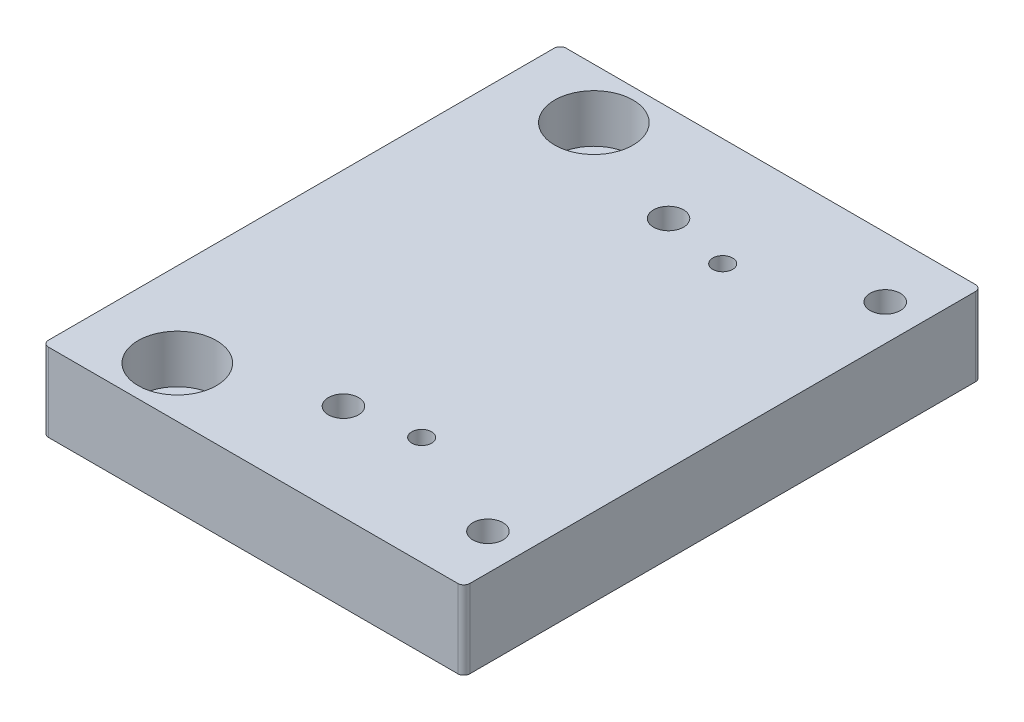
SolidWorks part; units mm, degrees
ref_plane "Front Plane" through (0, 0, 0) normal (0, 0, 1) x (1, 0, 0)
ref_plane "Top Plane" through (0, 0, 0) normal (0, 1, 0) x (1, 0, 0)
ref_plane "Right Plane" through (0, 0, 0) normal (1, 0, 0) x (0, 0, -1)
sketch "Sketch1" plane through (0, 0, 0) normal (0, 1, 0) x (1, 0, 0)
  line L1 (0, 0) -> (70, 0)
  line L2 (0, 0) -> (0, -86)
  line L3 (0, -86) -> (70, -86)
  line L4 (70, 0) -> (70, -86)
  dimension "D1" = 70
  dimension "D2" = 86
extrude "Boss-Extrude1" add sketch "Sketch1" along normal blind 5
sketch "Sketch2" plane through (0, 5, 0) normal (0, 1, 0) x (1, 0, 0)
  line L0 (0, -86) -> (70, -86) construction
  line L1 (70, 0) -> (58, 0)
  line L2 (70, 0) -> (70, -86)
  line L3 (70, -86) -> (58, -86)
  line L4 (58, 0) -> (58, -86)
  dimension "D1" = 12
extrude "Boss-Extrude2" add sketch "Sketch2" along normal blind 87
sketch "Sketch4" plane through (58, 0, 0) normal (-1, 0, 0) x (0, 0, 1)
  circle A0 centre (43, 56) radius 38
  dimension "D1" = 76
extrude "Cut-Extrude2" cut sketch "Sketch4" against normal blind 3
sketch "Sketch5" plane through (58, 0, 0) normal (-1, 0, 0) x (0, 0, 1)
  circle A0 centre (77.8, 90.8) radius 2.6
  circle A1 centre (77.8, 21.2) radius 2.6
  circle A2 centre (8.2, 90.8) radius 2.6
  circle A3 centre (8.2, 21.2) radius 2.6
  dimension "D1" = 5.2
extrude "Cut-Extrude3" cut sketch "Sketch5" against normal through all
fillet "Fillet1" radius 3 2 edges at (64, 92, 86) (64, 92, 0)
sketch "Sketch6" plane through (58, 0, 0) normal (-1, 0, 0) x (0, 0, 1)
  circle A0 centre (43, 56) radius 20
  dimension "D1" = 40
extrude "Cut-Extrude4" cut sketch "Sketch6" against normal through all
sketch "Sketch7" plane through (0, 0, 86) normal (0, 0, 1) x (1, 0, 0)
  line L1 (58, 5) -> (70, 5)
  line L2 (58, 5) -> (58, 92)
  line L3 (58, 92) -> (70, 92)
  line L4 (70, 5) -> (70, 92)
extrude "Cut-Extrude5" cut sketch "Sketch7" against normal through all
sketch "Sketch8" plane through (0, 0, 0) normal (0, -1, 0) x (1, 0, 0)
  line L0 (0, 43) -> (71.4574, 43) construction
  line L1 (0, 0) -> (0, 86) construction
  circle A0 centre (45, 68) radius 1.65
  circle A1 centre (45, 18) radius 1.65
  dimension "D1" = 25
  dimension "D2" = 3.3
  dimension "D3" = 45
sketch "Sketch9" plane through (0, 5, 0) normal (0, 1, 0) x (1, 0, 0)
  line L0 (70, 0) -> (70, -86) construction
  line L1 (70, 0) -> (0, 0) construction
  line L2 (70, -43) -> (0, -43) construction
  line L3 (0, 0) -> (0, -86) construction
  line L4 (40, -1) -> (40, -85) construction
  circle A0 centre (64, -10) radius 2.5
  circle A1 centre (64, -76) radius 2.5
  circle A2 centre (34, -70) radius 2.5
  circle A3 centre (34, -16) radius 2.5
  dimension "D1" = 6
  dimension "D2" = 10
  dimension "D3" = 5
  dimension "D4" = 6
  dimension "D5" = 27
  dimension "D6" = 27
fillet "Fillet2" radius 1 4 edges at (70, 2.5, 86) (70, 2.5, 0) (0, 2.5, 0) (0, 2.5, 86)
sketch "Sketch12" plane through (0, 0, 0) normal (0, -1, 0) x (1, 0, 0)
  line L0 (70, 1) -> (70, 85)
  line L1 (69, 86) -> (1, 86)
  line L2 (0, 85) -> (0, 1)
  line L3 (1, 0) -> (69, 0)
  line L4 (70, 1) -> (70, 85)
  line L5 (69, 86) -> (1, 86)
  line L6 (0, 85) -> (0, 1)
  line L7 (1, 0) -> (69, 0)
  line L8 (70, 1) -> (70, 85) construction
  line L9 (69, 86) -> (1, 86) construction
  line L10 (0, 85) -> (0, 1) construction
  line L11 (1, 0) -> (69, 0) construction
  arc A0 (70, 85) -> (69, 86) centre (69, 85) ccw
  arc A1 (1, 86) -> (0, 85) centre (1, 85) ccw
  arc A2 (0, 1) -> (1, 0) centre (1, 1) ccw
  arc A3 (69, 0) -> (70, 1) centre (69, 1) ccw
  arc A4 (70, 85) -> (69, 86) centre (69, 85) ccw
  arc A5 (1, 86) -> (0, 85) centre (1, 85) ccw
  arc A6 (0, 1) -> (1, 0) centre (1, 1) ccw
  arc A7 (69, 0) -> (70, 1) centre (69, 1) ccw
  arc A8 (70, 85) -> (69, 86) centre (69, 85) ccw construction
  arc A9 (1, 86) -> (0, 85) centre (1, 85) ccw construction
  arc A10 (0, 1) -> (1, 0) centre (1, 1) ccw construction
  arc A11 (69, 0) -> (70, 1) centre (69, 1) ccw construction
  dimension "D1" = 0
  dimension "D2" = 0
extrude "Boss-Extrude4" add sketch "Sketch12" along normal blind 8
sketch "Sketch3" plane through (0, 5, 0) normal (0, 1, 0) x (1, 0, 0)
  line L0 (0, -43) -> (62.3366, -43) construction
  line L1 (0, -1) -> (0, -85) construction
  circle A0 centre (14, -8.4) radius 3
  circle A1 centre (14, -77.6) radius 3
  dimension "D1" = 34.6
  dimension "D2" = 6
  dimension "D3" = 14
extrude "Cut-Extrude1" cut sketch "Sketch3" against normal through all
sketch "Sketch14" plane through (0, 5, 0) normal (0, 1, 0) x (1, 0, 0)
  circle A0 centre (14, -8.4) radius 6.5
  circle A1 centre (14, -77.6) radius 6.5
  dimension "D1" = 13
extrude "Cut-Extrude6" cut sketch "Sketch8" against normal through all and the other way through all
extrude "Cut-Extrude7" cut sketch "Sketch9" against normal through all
extrude "Cut-Extrude8" cut sketch "Sketch14" against normal blind 8
